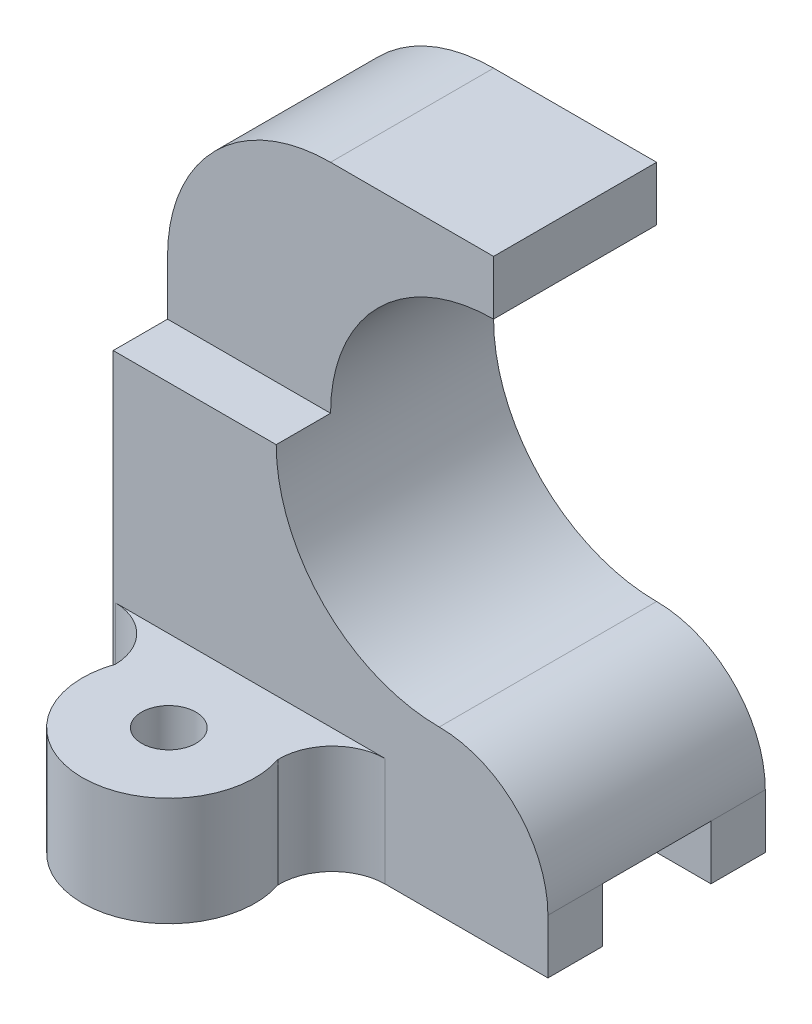
SolidWorks part; units mm, degrees
ref_plane "Front Plane" through (0, 0, 0) normal (0, 0, 1) x (1, 0, 0)
ref_plane "Top Plane" through (0, 0, 0) normal (0, 1, 0) x (1, 0, 0)
ref_plane "Right Plane" through (0, 0, 0) normal (1, 0, 0) x (0, 0, -1)
sketch "Sketch1" plane through (0, 0, 0) normal (0, 1, 0) x (1, 0, 0)
  line L1 (-40, -20) -> (40, -20)
  line L2 (-40, -20) -> (-40, 20)
  line L3 (-40, 20) -> (40, 20)
  line L4 (40, -20) -> (40, 20)
  line L5 (-40, -20) -> (40, 20) construction
  line L6 (-40, 20) -> (40, -20) construction
  point P0 (0, 0)
extrude "Boss-Extrude1" add sketch "Sketch1" along normal blind 100
sketch "Sketch2" plane through (0, 0, 20) normal (0, 0, 1) x (1, 0, 0)
  line L0 (40, 0) -> (40, 10)
  line L1 (40, 100) -> (40, 0) construction
  line L2 (20, 100) -> (-10, 100)
  line L3 (-40, 100) -> (40, 100) construction
  line L4 (-40, 100) -> (-40, 0) construction
  line L5 (-40, 70) -> (-40, 0)
  line L6 (-40, 0) -> (40, 0)
  line L7 (40, 0) -> (40, 10)
  line L8 (20, 90) -> (20, 100)
  arc A0 (40, 10) -> (20, 30) centre (20, 10) ccw
  arc A1 (20, 30) -> (20, 90) centre (20, 60) cw
  arc A2 (-10, 100) -> (-40, 70) centre (-10, 70) ccw
  line M2 (40, 0) -> (40, 100)
  line M3 (40, 100) -> (-40, 100)
  line M4 (-40, 100) -> (-40, 0)
  dimension "D1" = 10
  dimension "D5" = 30
  dimension "D2" = 10
  dimension "D3" = 20
  dimension "D4" = 20
  dimension "D6" = 30
  dimension "D7" = 70
extrude "Cut-Extrude1" cut sketch "Sketch2" against normal blind 100 contours A1 A0 L8 M2 M3 | A2 M3 M4
sketch "Sketch4" plane through (40, 0, 0) normal (1, 0, 0) x (0, 0, -1)
  line L0 (-20, 0) -> (20, 0) construction
  line L1 (-10, 0) -> (10, 0)
  line L2 (-10, 0) -> (-10, 10)
  line L3 (-10, 10) -> (10, 10)
  line L4 (10, 0) -> (10, 10)
  line L5 (20, 10) -> (-20, 10) construction
  line L6 (-20, 10) -> (-20, 0) construction
  line L7 (20, 10) -> (20, 0) construction
  dimension "D1" = 10
  dimension "D2" = 10
extrude "Cut-Extrude2" cut sketch "Sketch4" against normal blind 100
sketch "Sketch5" plane through (20, 0, 0) normal (1, 0, 0) x (0, 0, -1)
  line L1 (-20, 100) -> (-10, 100)
  line L2 (-20, 100) -> (-20, 60)
  line L3 (-20, 60) -> (-10, 60)
  line L4 (-10, 100) -> (-10, 60)
extrude "Cut-Extrude3" cut sketch "Sketch5" against normal blind 100
sketch "Sketch7" plane through (0, 0, 0) normal (0, 1, 0) x (1, 0, 0)
  line L0 (-40, -20) -> (-10, -20) construction
  line L1 (-10, -20) -> (20, -20) construction
  line L2 (-40, -20) -> (10, -20)
  arc A0 (-40, -20) -> (-29.8021, -29.7981) centre (-39.8001, -29.998) cw
  arc A1 (-29.8021, -29.7981) -> (0.3349, -30) centre (-14.7677, -34.9982) ccw
  arc A2 (10, -20) -> (0.3349, -30) centre (10.1309, -29.7972) ccw
  circle A3 centre (-14.7677, -34.9982) radius 5
  point P4 (-15, -20)
  point P5 (-14.7677, -34.9982)
  point P10 (10, -20)
  point P11 (10.1309, -29.7972)
  point P19 (0.3349, -30)
  dimension "D1" = 10
  dimension "D4" = 30
  dimension "D5" = 10
  dimension "D2" = 25
  dimension "D3" = 15
extrude "Boss-Extrude2" add sketch "Sketch7" along normal blind 20 contours A2 L2 A0 A1 A3
